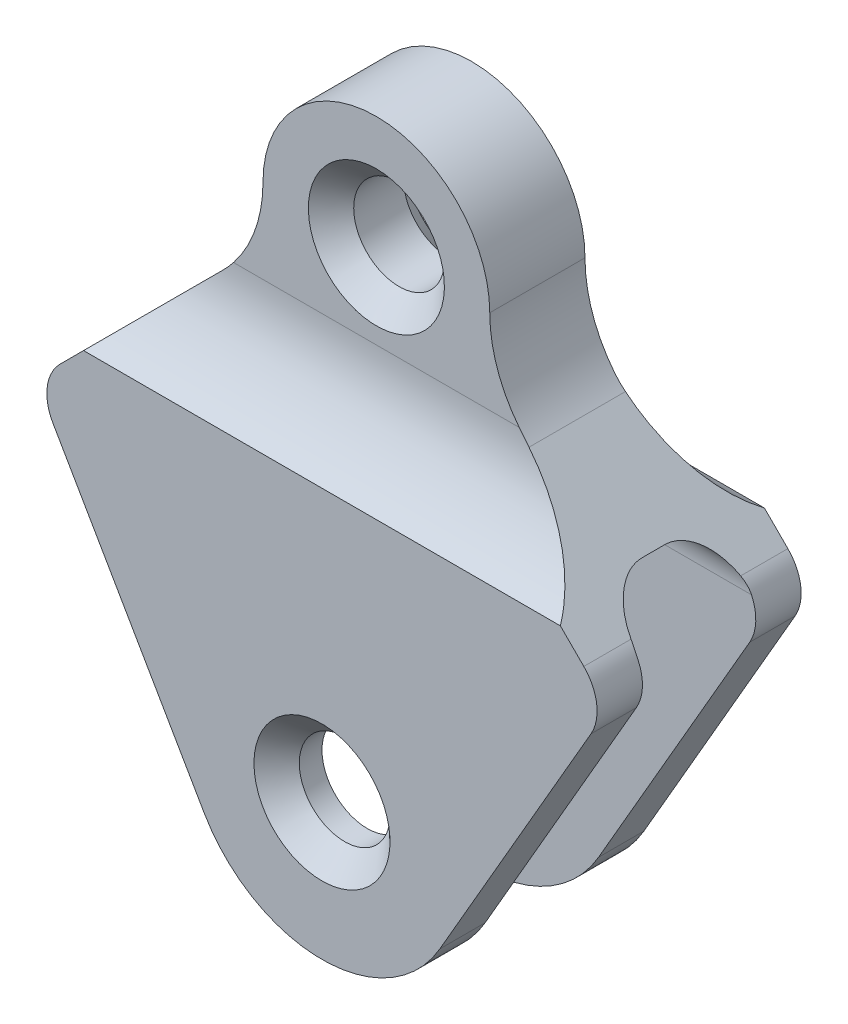
SolidWorks part; units mm, degrees
material "Titanium Ti-8Mn, Annealed"
ref_plane "Front Plane" through (0, 0, 0) normal (0, 0, 1) x (1, 0, 0)
ref_plane "Top Plane" through (0, 0, 0) normal (0, 1, 0) x (1, 0, 0)
ref_plane "Right Plane" through (0, 0, 0) normal (1, 0, 0) x (0, 0, -1)
sketch "Sketch1" plane through (0, 0, 0) normal (0, 0, 1) x (1, 0, 0)
  line L0 (33.7868, -21.2132) -> (57.7405, -45.1669)
  line L1 (59.3297, -57.238) -> (25.9808, -115)
  line L4 (0, 0) -> (0, -65.3003) construction
  line L5 (-59.3297, -57.238) -> (-25.9808, -115)
  line L6 (-33.7868, -21.2132) -> (-57.7405, -45.1669)
  arc A0 (57.7405, -45.1669) -> (59.3297, -57.238) centre (50.6694, -52.238) cw
  arc A1 (25.9808, -115) -> (-25.9808, -115) centre (0, -100) cw
  arc A4 (-57.7405, -45.1669) -> (-59.3297, -57.238) centre (-50.6694, -52.238) ccw
  arc A7 (-33.7868, -21.2132) -> (-25, 0) centre (-55, 0) ccw
  arc A8 (-25, 0) -> (25, 0) centre (0, 0) cw
  arc A9 (33.7868, -21.2132) -> (25, 0) centre (55, 0) cw
  circle A10 centre (0, -100) radius 10
  circle A11 centre (0, 0) radius 10
  dimension "D1" = 30
  dimension "D2" = 30
  dimension "D3" = 10
  dimension "D7" = 25
  dimension "D8" = 20
  dimension "D9" = 20
  dimension "D4" = 90
  dimension "D5" = 60
  dimension "D6" = 100
extrude "Boss-Extrude1" add sketch "Sketch1" along normal blind 45
sketch "Sketch2" plane through (0, 0, 0) normal (1, 0, 0) x (0, 0, -1)
  line L0 (-35, -130) -> (-35, -48)
  line L1 (-45, -130) -> (0, -130) construction
  line L2 (-25, -38) -> (-20, -38)
  line L3 (-10, -48) -> (-10, -130)
  line L4 (-10, -130) -> (-35, -130)
  line L5 (0, -130) -> (0, -115) construction
  line L6 (-22.5, 25) -> (-22.5, 3.6252) construction
  line L7 (0, 25) -> (-45, 25) construction
  line L8 (-12, 25) -> (-12, -18.6458)
  line L9 (0, -45.1669) -> (0, -21.2132) construction
  line L10 (0, -40) -> (0, 25)
  line L11 (0, 25) -> (-12, 25)
  line L12 (-33, 25) -> (-33, -18.6458)
  line L13 (-45, -40) -> (-45, 25)
  line L14 (-45, 25) -> (-33, 25)
  arc A0 (-35, -48) -> (-25, -38) centre (-25, -48) cw
  arc A1 (-20, -38) -> (-10, -48) centre (-20, -48) cw
  arc A2 (-12, -18.6458) -> (0, -40) centre (13, -18.6458) ccw
  arc A3 (-33, -18.6458) -> (-45, -40) centre (-58, -18.6458) cw
  point P17 (-22.5, 25)
  point P30 (-33.5443, 16.0881)
  point P31 (-22.5, 25)
  point P32 (-22.5, 25)
  dimension "D1" = 25
  dimension "D2" = 10
  dimension "D5" = 12
  dimension "D7" = 25
  dimension "D3" = 92
  dimension "D4" = 10
  dimension "D6" = 65
extrude "Cut-Extrude1" cut sketch "Sketch2" against normal through all both and the other way through all
chamfer "Chamfer1" distance 5 angle 45 4 edges at (0, -10, 12) (0, 10, 33) (10, -100, 0) (10, -100, 45)
